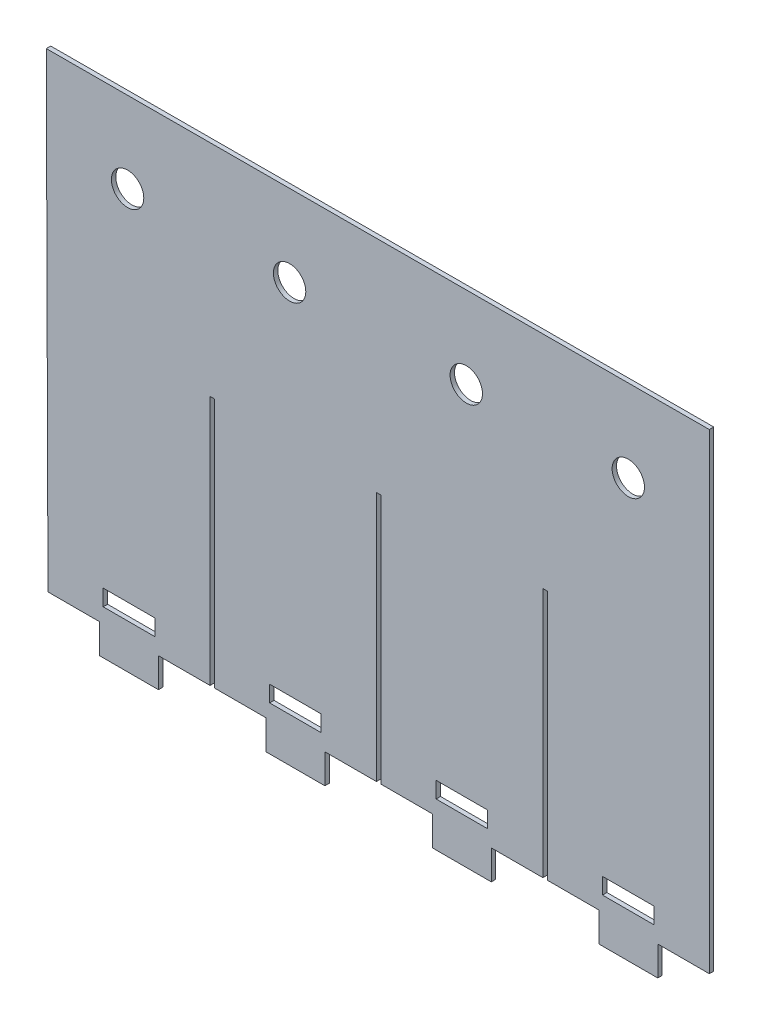
SolidWorks part; units mm, degrees
ref_plane "Front Plane" through (0, 0, 0) normal (0, 0, 1) x (1, 0, 0)
ref_plane "Top Plane" through (0, 0, 0) normal (0, 1, 0) x (1, 0, 0)
ref_plane "Right Plane" through (0, 0, 0) normal (1, 0, 0) x (0, 0, -1)
sketch "Sketch1" plane through (0, 0, 0) normal (0, 0, 1) x (1, 0, 0)
  line L0 (450.1677, -318.9167) -> (450.1677, 1.0833)
  line L1 (450.1677, 1.0833) -> (0, 0)
  line L2 (0, 0) -> (1.1677, -318.9167)
  line L4 (111.1677, -318.9167) -> (111.1677, -148.9167)
  line L5 (111.1677, -148.9167) -> (114.1677, -148.9167)
  line L6 (114.1677, -148.9167) -> (114.1677, -318.9167)
  line L8 (224.1677, -318.9167) -> (224.1677, -148.9167)
  line L9 (224.1677, -148.9167) -> (227.1677, -148.9167)
  line L10 (227.1677, -148.9167) -> (227.1677, -318.9167)
  line L12 (337.1677, -318.9167) -> (337.1677, -148.9167)
  line L13 (337.1677, -148.9167) -> (340.1677, -148.9167)
  line L14 (340.1677, -148.9167) -> (340.1677, -318.9167)
  line L16 (450.1677, -318.9167) -> (415.1677, -318.9167)
  line L17 (415.1677, -318.9167) -> (415.1677, -338.9167)
  line L18 (415.1677, -338.9167) -> (375.1677, -338.9167)
  line L19 (375.1677, -338.9167) -> (375.1677, -318.9167)
  line L20 (375.1677, -318.9167) -> (340.1677, -318.9167)
  line L21 (337.1677, -318.9167) -> (302.1677, -318.9167)
  line L22 (302.1677, -318.9167) -> (302.1677, -338.9167)
  line L23 (302.1677, -338.9167) -> (262.1677, -338.9167)
  line L24 (262.1677, -338.9167) -> (262.1677, -318.9167)
  line L25 (262.1677, -318.9167) -> (227.1677, -318.9167)
  line L26 (224.1677, -318.9167) -> (189.1677, -318.9167)
  line L27 (189.1677, -318.9167) -> (189.1677, -338.9167)
  line L28 (189.1677, -338.9167) -> (149.1677, -338.9167)
  line L29 (149.1677, -338.9167) -> (149.1677, -318.9167)
  line L30 (149.1677, -318.9167) -> (114.1677, -318.9167)
  line L31 (1.1677, -318.9167) -> (36.1677, -318.9167)
  line L32 (36.1677, -318.9167) -> (36.1677, -338.9167)
  line L33 (36.1677, -338.9167) -> (76.1677, -338.9167)
  line L34 (76.1677, -338.9167) -> (76.1677, -318.9167)
  line L35 (76.1677, -318.9167) -> (111.1677, -318.9167)
  point P31 (0, 0)
  dimension "D1" = 110
  dimension "D2" = 320
  dimension "D3" = 3
  dimension "D4" = 40
  dimension "D5" = 170
  dimension "D6" = 20
extrude "Boss-Extrude1" add sketch "Sketch1" along normal blind 3 contours L0 L1 L2 L31 L32 L33 L34 L35 L4 L5 L6 L30 L29 L28 L27 L26 L8 L9 L10 L25 L24 L23 L22 L21 L12 L13 L14 L20 L19 L18 L17 L16
sketch "Sketch2" plane through (0, 0, 3) normal (0, 0, 1) x (1, 0, 0)
  line L0 (0, 0) -> (1.1677, -318.9167) construction
  line L2 (450.1677, -318.9167) -> (450.1677, 1.0833) construction
  line L9 (450.1677, 1.0833) -> (0, 0) construction
  circle A0 centre (55.2013, -54.8673) radius 11
  circle A1 centre (165.2013, -54.8673) radius 11
  circle A2 centre (285.1677, -54.8673) radius 11
  circle A3 centre (395.1677, -54.8673) radius 11
  point P4 (0, 0)
  point P7 (0, 0)
  point P8 (0, 0)
  point P11 (0, 0)
  point P17 (54.0369, -51.2883)
  point P18 (0, 0)
  dimension "D1" = 22
  dimension "D2" = 55
  dimension "D3" = 55
  dimension "D4" = 55
  dimension "D5" = 110
  dimension "D6" = 110
extrude "Cut-Extrude1" cut sketch "Sketch2" against normal blind 3
sketch "Sketch3" plane through (0, 0, 3) normal (0, 0, 1) x (1, 0, 0)
  line L0 (415.1677, -318.9167) -> (415.1677, -338.9167) construction
  line L1 (377.6677, -297.9167) -> (412.6677, -297.9167)
  line L2 (377.6677, -297.9167) -> (377.6677, -308.9167)
  line L3 (377.6677, -308.9167) -> (412.6677, -308.9167)
  line L4 (412.6677, -297.9167) -> (412.6677, -308.9167)
  line L5 (151.6677, -297.9167) -> (186.6677, -297.9167)
  line L6 (375.1677, -318.9167) -> (340.1677, -318.9167) construction
  line L7 (264.6677, -297.9167) -> (299.6677, -297.9167)
  line L8 (264.6677, -297.9167) -> (264.6677, -308.9167)
  line L9 (264.6677, -308.9167) -> (299.6677, -308.9167)
  line L10 (299.6677, -297.9167) -> (299.6677, -308.9167)
  line L11 (151.6677, -297.9167) -> (151.6677, -308.9167)
  line L12 (151.6677, -308.9167) -> (186.6677, -308.9167)
  line L13 (186.6677, -297.9167) -> (186.6677, -308.9167)
  line L14 (38.6677, -297.9167) -> (73.6677, -297.9167)
  line L15 (38.6677, -297.9167) -> (38.6677, -308.9167)
  line L16 (38.6677, -308.9167) -> (73.6677, -308.9167)
  line L17 (73.6677, -297.9167) -> (73.6677, -308.9167)
  line L18 (302.1677, -318.9167) -> (302.1677, -338.9167) construction
  line L19 (189.1677, -318.9167) -> (189.1677, -338.9167) construction
  line L20 (36.1677, -318.9167) -> (36.1677, -338.9167) construction
  dimension "D1" = 11
  dimension "D2" = 35
  dimension "D3" = 2.5
  dimension "D4" = 10
  dimension "D5" = 2.5
  dimension "D6" = 2.5
  dimension "D7" = 2.5
extrude "Cut-Extrude2" cut sketch "Sketch3" against normal blind 3
